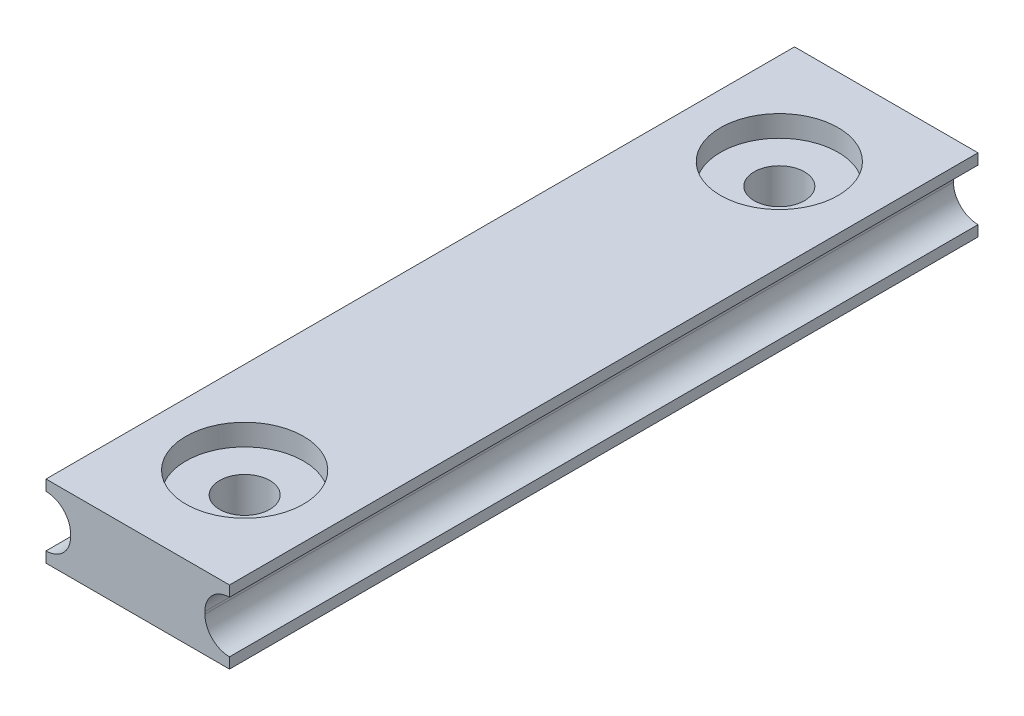
SolidWorks part; units mm, degrees
ref_plane "Front Plane" through (0, 0, 0) normal (0, 0, 1) x (1, 0, 0)
ref_plane "Top Plane" through (0, 0, 0) normal (0, 1, 0) x (1, 0, 0)
ref_plane "Right Plane" through (0, 0, 0) normal (1, 0, 0) x (0, 0, -1)
sketch "Sketch1" plane through (0, 0, 0) normal (0, 0, 1) x (1, 0, 0)
  line L0 (0, 0) -> (0, 2.8653) construction
  line L1 (0, 0) -> (3.9378, 0) construction
  line L2 (-3.14, 0.055) -> (-3.14, -0.055)
  line L3 (-4.29, 1.705) -> (4.29, 1.705)
  line L4 (-4.29, 1.705) -> (-4.29, 1.205)
  line L5 (-4.29, -1.705) -> (4.29, -1.705)
  line L6 (4.29, 1.705) -> (4.29, 1.205)
  line L7 (3.14, 0.055) -> (3.14, -0.055)
  line L8 (4.29, -1.205) -> (4.29, -1.705)
  line L9 (-4.29, -1.205) -> (-4.29, -1.705)
  arc A0 (3.14, 0.055) -> (4.29, 1.205) centre (4.29, 0.055) cw
  arc A1 (3.14, -0.055) -> (4.29, -1.205) centre (4.29, -0.055) ccw
  arc A2 (-3.14, 0.055) -> (-4.29, 1.205) centre (-4.29, 0.055) ccw
  arc A3 (-3.14, -0.055) -> (-4.29, -1.205) centre (-4.29, -0.055) cw
  dimension "D5" = 1.15
  dimension "D1" = 8.58
  dimension "D2" = 3.41
  dimension "D3" = 0.11
  dimension "D4" = 6.28
extrude "Boss-Extrude1" add sketch "Sketch1" along normal mid plane 35
sketch "Sketch2" plane through (0, 1.705, 0) normal (0, 1, 0) x (1, 0, 0)
  line L1 (0, 0) -> (0, 6.7591) construction
  line L2 (4.29, 17.5) -> (-4.29, 17.5) construction
  circle A0 centre (0, 12.5) radius 1.175
  dimension "D1" = 2.35
  dimension "D2" = 5
extrude "Cut-Extrude1" cut sketch "Sketch2" against normal through all
sketch "Sketch3" plane through (0, 1.705, 0) normal (0, 1, 0) x (1, 0, 0)
  circle A0 centre (0, 12.5) radius 2.75
  dimension "D1" = 5.5
extrude "Cut-Extrude2" cut sketch "Sketch3" against normal blind 1
mirror "Mirror1" about plane through (0, 0, 0) normal (0, 0, 1) of "Cut-Extrude2", "Cut-Extrude1"
